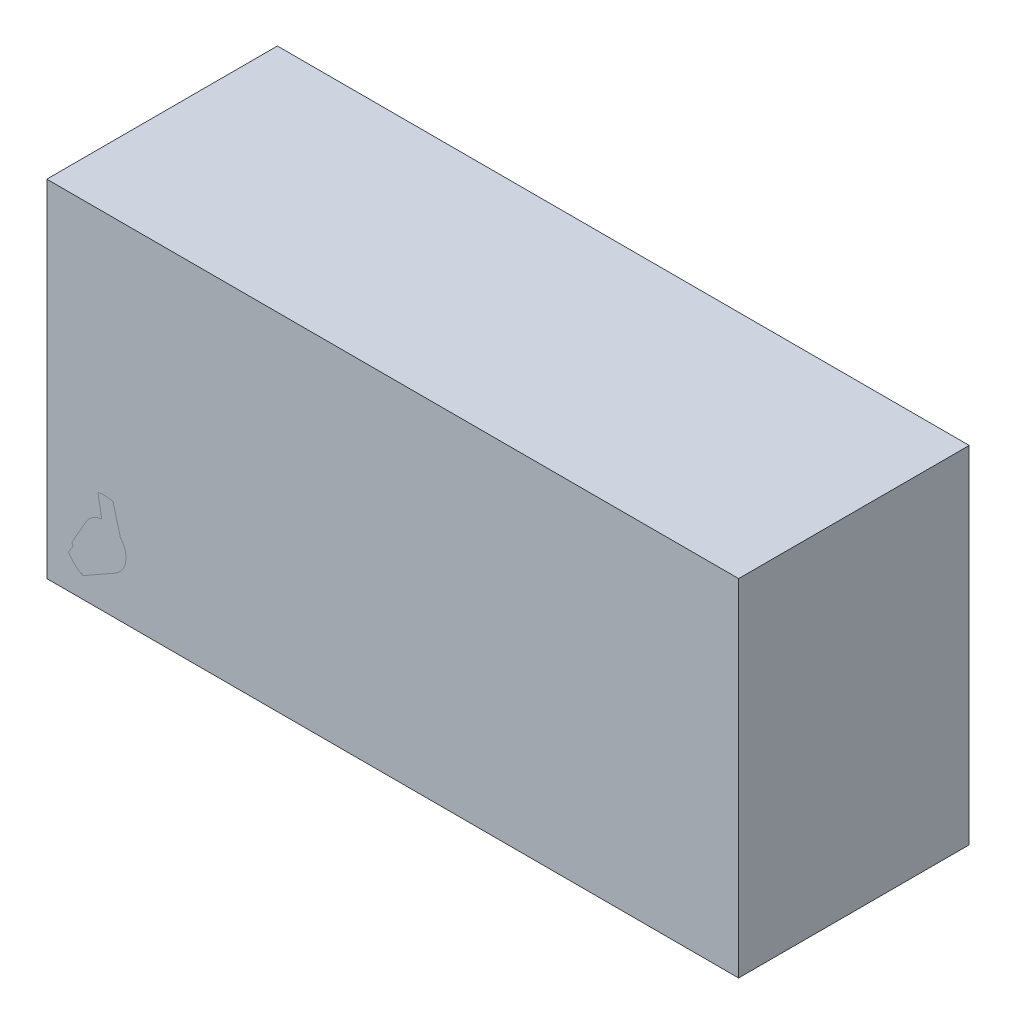
SolidWorks part; units mm, degrees
other "Load"
ref_plane "Front Plane" through (0, 0, 0) normal (0, 0, 1) x (1, 0, 0)
ref_plane "Top Plane" through (0, 0, 0) normal (0, 1, 0) x (1, 0, 0)
ref_plane "Right Plane" through (0, 0, 0) normal (1, 0, 0) x (0, 0, -1)
sketch "Sketch1" plane through (0, 0, 0) normal (0, 0, 1) x (1, 0, 0)
  line L1 (-76.2, -38.1) -> (76.2, -38.1)
  line L2 (-76.2, -38.1) -> (-76.2, 38.1)
  line L3 (-76.2, 38.1) -> (76.2, 38.1)
  line L4 (76.2, -38.1) -> (76.2, 38.1)
  line L5 (-76.2, -38.1) -> (76.2, 38.1) construction
  line L6 (-76.2, 38.1) -> (76.2, -38.1) construction
  point P0 (0, 0)
  dimension "D1" = 152.4
  dimension "D2" = 76.2
extrude "Boss-Extrude1" add sketch "Sketch1" along normal blind 50.8
sketch "Sketch2" plane through (0, 0, 50.8) normal (0, 0, 1) x (1, 0, 0)
  line L0 (-76.2, -38.1) -> (76.2, -38.1) construction
  line L1 (-76.2, 38.1) -> (-76.2, -38.1) construction
  circle A0 centre (-63.5, -25.4) radius 4.7625
  dimension "D1" = 9.525
  dimension "D2" = 12.7
  dimension "D3" = 12.7
extrude "Cut-Extrude1" cut sketch "Sketch2" against normal blind 12.7
sketch "Sketch3" plane through (0, 0, 0) normal (0, 0, -1) x (-1, 0, 0)
  line L0 (-76.2, 38.1) -> (76.2, 38.1) construction
  circle A0 centre (63.5, 25.4) radius 4.7625
  circle A1 centre (-63.5, 25.4) radius 4.7625
  dimension "D1" = 9.525
  dimension "D2" = 63.5
  dimension "D3" = 63.5
  dimension "D4" = 12.7
  dimension "D5" = 12.7
extrude "Cut-Extrude2" cut sketch "Sketch3" against normal blind 12.7
sketch "Sketch4" plane through (0, 0, 50.8) normal (0, 0, 1) x (1, 0, 0)
  circle A2 centre (-63.5, -25.4) radius 9.525
  circle A3 centre (-63.5, -25.4) radius 9.525
  dimension "D1" = 4.7625
extrude "Boss-Extrude2" add sketch "Sketch4" against normal blind 12.7 separate body
